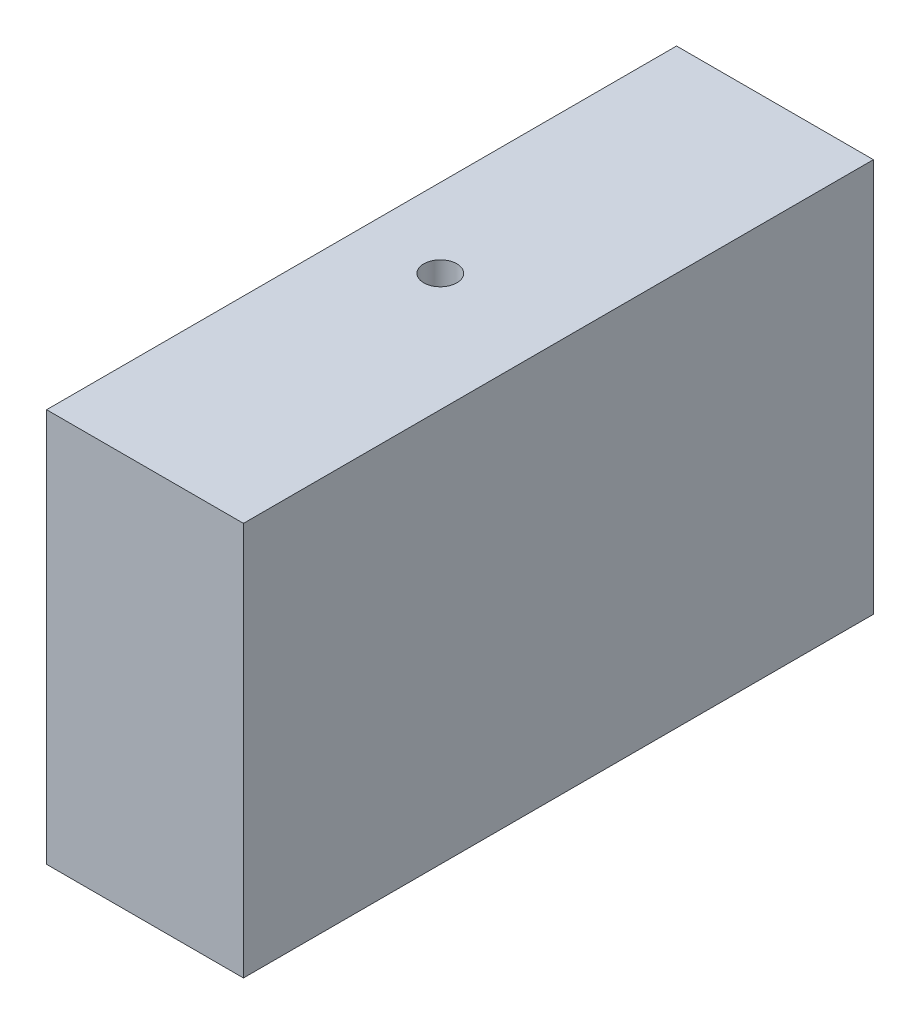
SolidWorks part; units mm, degrees
ref_plane "Alzado" through (0, 0, 0) normal (0, 0, 1) x (1, 0, 0)
ref_plane "Planta" through (0, 0, 0) normal (0, 1, 0) x (1, 0, 0)
ref_plane "Vista lateral" through (0, 0, 0) normal (1, 0, 0) x (0, 0, -1)
sketch "Croquis1" plane through (0, 0, 0) normal (0, 0, 1) x (1, 0, 0)
  line L0 (-31.6318, 32.3062) -> (-6.6318, 32.3062)
  line L1 (-6.6318, 32.3062) -> (-6.6318, -17.6938)
  line L2 (-6.6318, -17.6938) -> (-31.6318, -17.6938)
  line L3 (-31.6318, -17.6938) -> (-31.6318, 32.3062)
extrude "Saliente-Extruir1" add sketch "Croquis1" along normal blind 80
hole_wizard "Perforador para roscar para macho de roscar para M5x0.81" positions "Croquis3D2" profile "Croquis3" hole size "M5x0.8" standard "Ansi Metric"
sketch3d "Croquis3D2"
  line L0 (-31.6318, 32.3062, 80) -> (-31.6318, 32.3062, 0) construction
  line L1 (-6.6318, 32.3062, 0) -> (-31.6318, 32.3062, 0) construction
  point P0 (-21.6318, 32.3062, 40)
  dimension "D1" = 10
  dimension "D2" = 40
sketch "Croquis3" plane through (-21.6318, 32.3062, 40) normal (1, 0, 0) x (0, 0, 1)
  line L0 (0, 0) -> (0, 12.2618)
  line L1 (0, 12.2618) -> (2.1, 11)
  line L2 (2.1, 11) -> (2.1, 0)
  line L5 (2.1, 0) -> (0, 0)
  line L10 (0, 12.2618) -> (-2.1, 11) construction
  line L11 (0, -6.35) -> (0, 107.95) construction
  dimension "Diámetro de taladro" = 4.2
  dimension "Profundidad de taladro" = 11
  dimension "Ángulo de perforador" = 118
hole_wizard "Perforador para roscar para macho de roscar para M5x0.82" positions "Croquis3D3" profile "Croquis4" hole size "M5x0.8" standard "Ansi Metric"
sketch3d "Croquis3D3"
  line L0 (-6.6318, -17.6938, 80) -> (-6.6318, -17.6938, 0) construction
  line L1 (-31.6318, -17.6938, 0) -> (-6.6318, -17.6938, 0) construction
  point P0 (-21.6318, -17.6938, 40)
  dimension "D1" = 15
  dimension "D2" = 40
sketch "Croquis4" plane through (-21.6318, -17.6938, 40) normal (1, 0, 0) x (0, 0, -1)
  line L0 (0, 0) -> (0, 12.2618)
  line L1 (0, 12.2618) -> (2.1, 11)
  line L2 (2.1, 11) -> (2.1, 0)
  line L5 (2.1, 0) -> (0, 0)
  line L10 (0, 12.2618) -> (-2.1, 11) construction
  line L11 (0, -6.35) -> (0, 107.95) construction
  dimension "Diámetro de taladro" = 4.2
  dimension "Profundidad de taladro" = 11
  dimension "Ángulo de perforador" = 118
